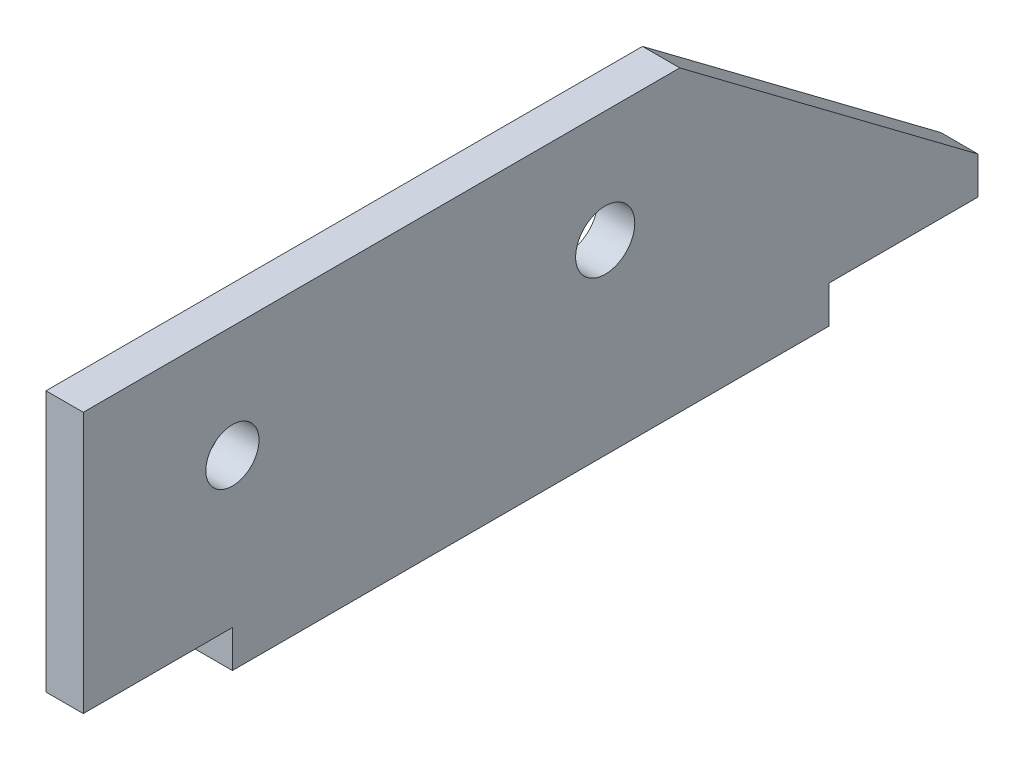
SolidWorks part; units mm, degrees
ref_plane "Front Plane" through (0, 0, 0) normal (0, 0, 1) x (1, 0, 0)
ref_plane "Top Plane" through (0, 0, 0) normal (0, 1, 0) x (1, 0, 0)
ref_plane "Right Plane" through (0, 0, 0) normal (1, 0, 0) x (0, 0, -1)
sketch "Sketch1" plane through (0, 0, 0) normal (1, 0, 0) x (0, 0, -1)
  line L0 (50.8, 25.4) -> (76.2, 6.35)
  line L1 (0, 0) -> (76.2, 0)
  line L2 (0, 0) -> (0, 25.4)
  line L3 (76.2, 6.35) -> (76.2, 0)
  line L4 (50.8, 25.4) -> (0, 25.4)
  dimension "D1" = 50.8
  dimension "D2" = 6.35
  dimension "D3" = 25.4
  dimension "D4" = 76.2
extrude "Boss-Extrude1" add sketch "Sketch1" along normal blind 3.175
sketch "Sketch2" plane through (3.175, 0, 0) normal (1, 0, 0) x (0, 0, -1)
  line L0 (0, 0) -> (76.2, 0) construction
  line L1 (12.7, 15.875) -> (44.45, 15.875) construction
  line L2 (0, 25.4) -> (0, 0) construction
  line L4 (0, 0) -> (12.7, 0)
  line L5 (0, 0) -> (0, 3.175)
  line L6 (0, 3.175) -> (12.7, 3.175)
  line L7 (12.7, 0) -> (12.7, 3.175)
  line L8 (76.2, 0) -> (63.5, 0)
  line L9 (76.2, 0) -> (76.2, 3.175)
  line L10 (76.2, 3.175) -> (63.5, 3.175)
  line L11 (63.5, 0) -> (63.5, 3.175)
  circle A0 centre (12.7, 15.875) radius 2.2647
  circle A1 centre (44.45, 15.875) radius 2.5193
  dimension "D1" = 15.875
  dimension "D2" = 31.75
  dimension "D3" = 12.7
  dimension "D4" = 12.7
  dimension "D5" = 12.7
  dimension "D6" = 3.175
extrude "Cut-Extrude1" cut sketch "Sketch2" against normal blind 3.175
